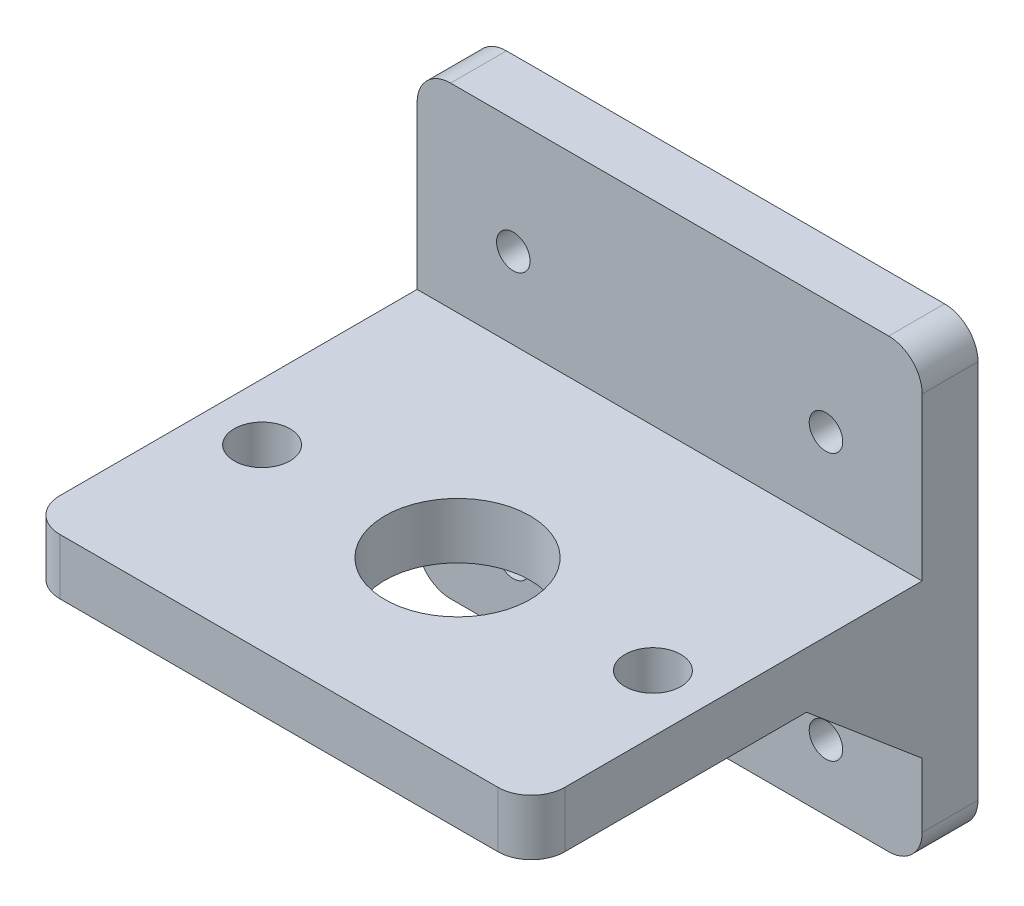
SolidWorks part; units mm, degrees
ref_plane "前视基准面" through (0, 0, 0) normal (0, 0, 1) x (1, 0, 0)
ref_plane "上视基准面" through (0, 0, 0) normal (0, 1, 0) x (1, 0, 0)
ref_plane "右视基准面" through (0, 0, 0) normal (1, 0, 0) x (0, 0, -1)
sketch "草图1" plane through (-84.8519, 0, -36.5617) normal (0, 1, 0) x (1, 0, 0)
  line L1 (811.5521, 171.5343) -> (856.7858, 171.5343)
  line L2 (811.5521, 171.5343) -> (811.5521, 211.5343)
  line L3 (811.5521, 211.5343) -> (856.7858, 211.5343)
  line L4 (856.7858, 171.5343) -> (856.7858, 211.5343)
extrude "凸台-拉伸1" add sketch "草图1" along normal blind 5
sketch "草图2" plane through (0, 0, 0) normal (0, -1, 0) x (-1, 0, 0)
  line L0 (-749.317, 208.096) -> (-749.317, 224.0984) construction
  line L1 (-726.7002, 208.096) -> (-771.9339, 208.096) construction
  line L3 (-749.317, 224.0984) -> (-766.817, 224.0984) construction
  circle A0 centre (-766.817, 224.0984) radius 2.5
  circle A1 centre (-731.817, 224.0984) radius 2.5
  circle A2 centre (-749.317, 224.0984) radius 6.5
extrude "切除-拉伸1" cut sketch "草图2" against normal through all
sketch "草图3" plane through (0, 0, -248.096) normal (0, 0, -1) x (-1, 0, 0)
  line L0 (-749.317, 0) -> (-749.317, 5) construction
  line L1 (-771.9339, 0) -> (-726.7002, 0) construction
  line L2 (-771.9339, 5) -> (-726.7002, 5) construction
  line L3 (-726.7002, 2.5) -> (-771.9339, 2.5) construction
  line L4 (-726.7002, 5) -> (-726.7002, 0) construction
  line L5 (-771.9339, 5) -> (-771.9339, 0) construction
  line L7 (-726.7002, -17.5) -> (-771.9339, -17.5)
  line L8 (-726.7002, -17.5) -> (-726.7002, 22.5)
  line L9 (-726.7002, 22.5) -> (-771.9339, 22.5)
  line L10 (-771.9339, -17.5) -> (-771.9339, 22.5)
  line L11 (-726.7002, -17.5) -> (-771.9339, 22.5) construction
  line L12 (-726.7002, 22.5) -> (-771.9339, -17.5) construction
  point P12 (-749.317, 2.5)
extrude "凸台-拉伸2" add sketch "草图3" against normal blind 5
sketch "草图4" plane through (726.7002, 0, 0) normal (-1, 0, 0) x (0, 0, 1)
  line L0 (-232.7383, 0) -> (-243.096, -8.75)
  line L1 (-243.096, 0) -> (-208.096, 0) construction
  line L2 (-243.096, -17.5) -> (-243.096, 0) construction
  line L3 (-243.096, -8.75) -> (-243.096, 0)
  line L4 (-243.096, 0) -> (-232.7383, 0)
  point P8 (-243.096, -8.75)
extrude "凸台-拉伸3" add sketch "草图4" against normal up to surface (45.2336 mm away) up to face at (771.9339, 2.5, -235.596)
fillet "圆角1" radius 3 2 edges at (771.9339, 2.5, -208.096) (726.7002, 2.5, -208.096)
fillet "圆角3" radius 3 4 edges at (726.7002, -17.5, -245.596) (771.9339, -17.5, -245.596) (726.7002, 22.5, -245.596) (771.9339, 22.5, -245.596)
sketch "草图5" plane through (0, 0, -243.096) normal (0, 0, 1) x (1, 0, 0)
  line L0 (749.317, 5) -> (749.317, 22.5) construction
  line L1 (726.7002, 5) -> (771.9339, 5) construction
  line L2 (729.7002, 22.5) -> (768.9339, 22.5) construction
  line L3 (726.7002, 12.25) -> (771.9339, 12.25) construction
  line L4 (726.7002, 5) -> (726.7002, 19.5) construction
  line L5 (771.9339, 19.5) -> (771.9339, 5) construction
  line L6 (771.9339, -11.625) -> (726.7002, -11.625) construction
  line L7 (771.9339, -8.75) -> (771.9339, -14.5) construction
  line L8 (726.7002, -14.5) -> (726.7002, -8.75) construction
  circle A0 centre (749.317, 12.25) radius 14 construction
  circle A1 centre (763.317, 12.25) radius 1.5
  circle A5 centre (749.317, -11.625) radius 14 construction
  circle A6 centre (763.317, -11.625) radius 1.5
  circle A7 centre (735.317, -11.625) radius 1.5
  circle A8 centre (735.317, 12.25) radius 1.5
  point P25 (755.5604, 18.4934)
extrude "切除-拉伸2" cut sketch "草图5" against normal through all
